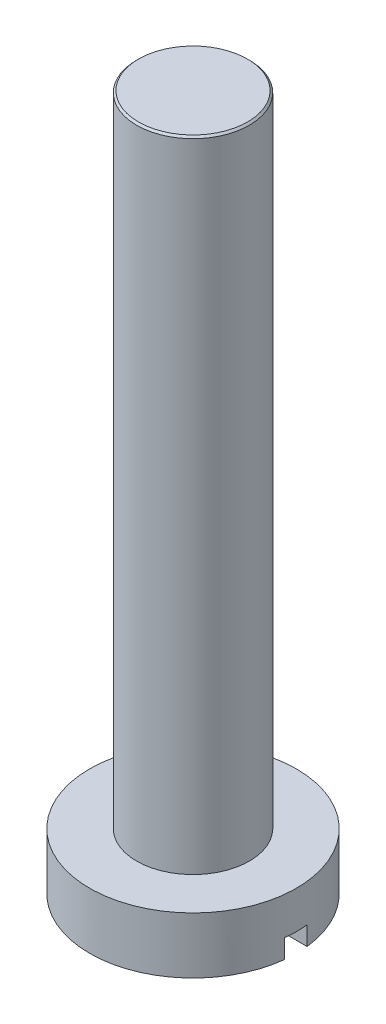
SolidWorks part; units mm, degrees
ref_plane "Front Plane" through (0, 0, 0) normal (0, 0, 1) x (1, 0, 0)
ref_plane "Top Plane" through (0, 0, 0) normal (0, 1, 0) x (1, 0, 0)
ref_plane "Right Plane" through (0, 0, 0) normal (1, 0, 0) x (0, 0, -1)
sketch "Sketch1" plane through (0, 0, 0) normal (0, 1, 0) x (1, 0, 0)
  circle A0 centre (0, 0) radius 1.5
  dimension "D1" = 3
extrude "Boss-Extrude1" add sketch "Sketch1" along normal blind 17
cosmetic thread "Cosmetic Thread1" parameters "D1"=11, "D2"=2.439
sketch "Sketch2" plane through (0, 0, 0) normal (0, -1, 0) x (1, 0, 0)
  circle A0 centre (0, 0) radius 2.75
  circle A1 centre (0, 0) radius 1.5
  circle A2 centre (0, 0) radius 1.5 construction
  dimension "D1" = 0
  dimension "D2" = 1.25
extrude "Boss-Extrude2" add sketch "Sketch2" along normal blind 1.5 separate body
sketch "Sketch3" plane through (0, -1.5, 0) normal (0, -1, 0) x (1, 0, 0)
  line L1 (-4.0982, -0.3) -> (4.0982, -0.3)
  line L2 (-4.0982, -0.3) -> (-4.0982, 0.3)
  line L3 (-4.0982, 0.3) -> (4.0982, 0.3)
  line L4 (4.0982, -0.3) -> (4.0982, 0.3)
  line L5 (-4.0982, -0.3) -> (4.0982, 0.3) construction
  line L6 (-4.0982, 0.3) -> (4.0982, -0.3) construction
  point P0 (0, 0)
  dimension "D1" = 0.6
extrude "Cut-Extrude1" cut sketch "Sketch3" against normal blind 0.5
chamfer "Chamfer1" distance 0.05 angle 45 1 edges at (0, 17, 1.5)
